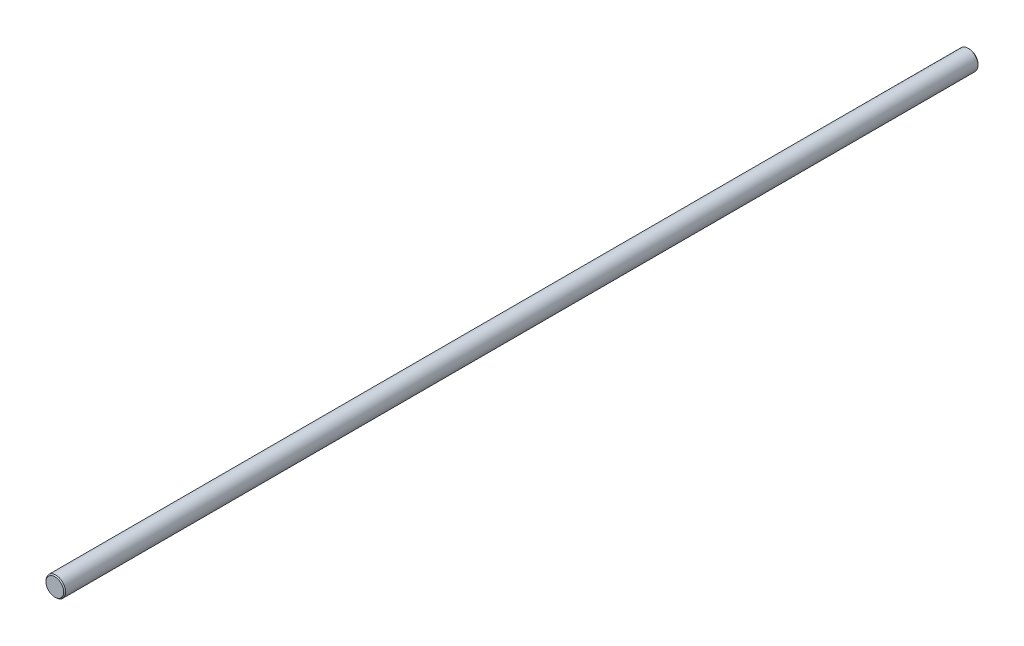
SolidWorks part; units mm, degrees
ref_plane "Front Plane" through (0, 0, 0) normal (0, 0, 1) x (1, 0, 0)
ref_plane "Top Plane" through (0, 0, 0) normal (0, 1, 0) x (1, 0, 0)
ref_plane "Right Plane" through (0, 0, 0) normal (1, 0, 0) x (0, 0, -1)
sketch "Sketch1" plane through (0, 0, 0) normal (0, 0, 1) x (1, 0, 0)
  circle A0 centre (0, 0) radius 5
  dimension "D1" = 10
extrude "Boss-Extrude1" add sketch "Sketch1" along normal blind 465
chamfer "Chamfer1" distance 0.5 angle 45 1 edges at (5, 0, 465)
chamfer "Chamfer2" distance 0.5 angle 45 1 edges at (5, 0, 0)
